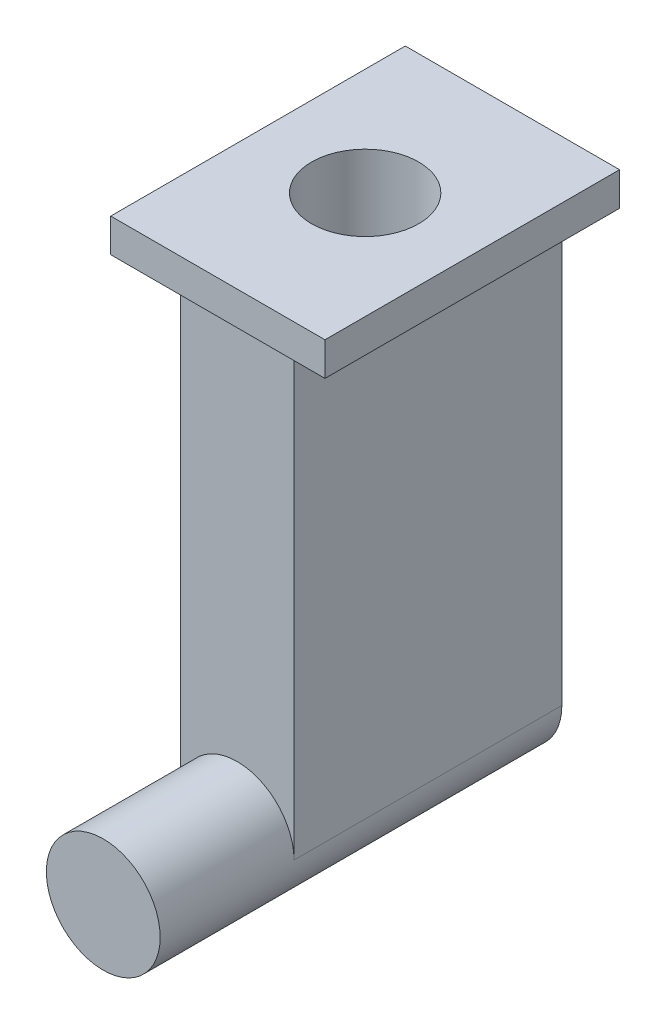
SolidWorks part; units mm, degrees
ref_plane "Front Plane" through (0, 0, 0) normal (0, 0, 1) x (1, 0, 0)
ref_plane "Top Plane" through (0, 0, 0) normal (0, 1, 0) x (1, 0, 0)
ref_plane "Right Plane" through (0, 0, 0) normal (1, 0, 0) x (0, 0, -1)
sketch "Sketch1" plane through (0, 0, 0) normal (0, 0, 1) x (1, 0, 0)
  circle A0 centre (0, 0) radius 42.5
  dimension "D1" = 85
extrude "Boss-Extrude1" add sketch "Sketch1" against normal blind 100
sketch "Sketch2" plane through (0, 0, -100) normal (0, 0, -1) x (-1, 0, 0)
  line L0 (-42.5, 350) -> (42.5, 350)
  line L2 (-42.5, 0) -> (-42.5, 350)
  line L4 (42.5, 0) -> (42.5, 350)
  arc A0 (-42.5, 0) -> (42.5, 0) centre (0, 0) ccw
  circle A1 centre (0, 0) radius 42.5 construction
  dimension "D1" = 350
extrude "Boss-Extrude2" add sketch "Sketch2" along normal blind 200
ref_plane "Plane1" through (0, 350, 0) normal (0, 1, 0) x (1, 0, 0)
sketch "Sketch5" plane through (0, 350, 104.4227) normal (0, 1, 0) x (1, 0, 0)
  line L7 (-80, 190) -> (80, 190)
  line L8 (-80, 190) -> (-80, 410)
  line L9 (-80, 410) -> (80, 410)
  line L10 (80, 190) -> (80, 410)
  point P12 (0, 300)
extrude "Boss-Extrude4" add sketch "Sketch5" along normal mid plane 25
sketch "Sketch6" plane through (0, 362.5, 104.4227) normal (0, 1, 0) x (1, 0, 0)
  circle A0 centre (0, 300) radius 40
  dimension "D1" = 80
extrude "Cut-Extrude1" cut sketch "Sketch6" against normal blind 250
